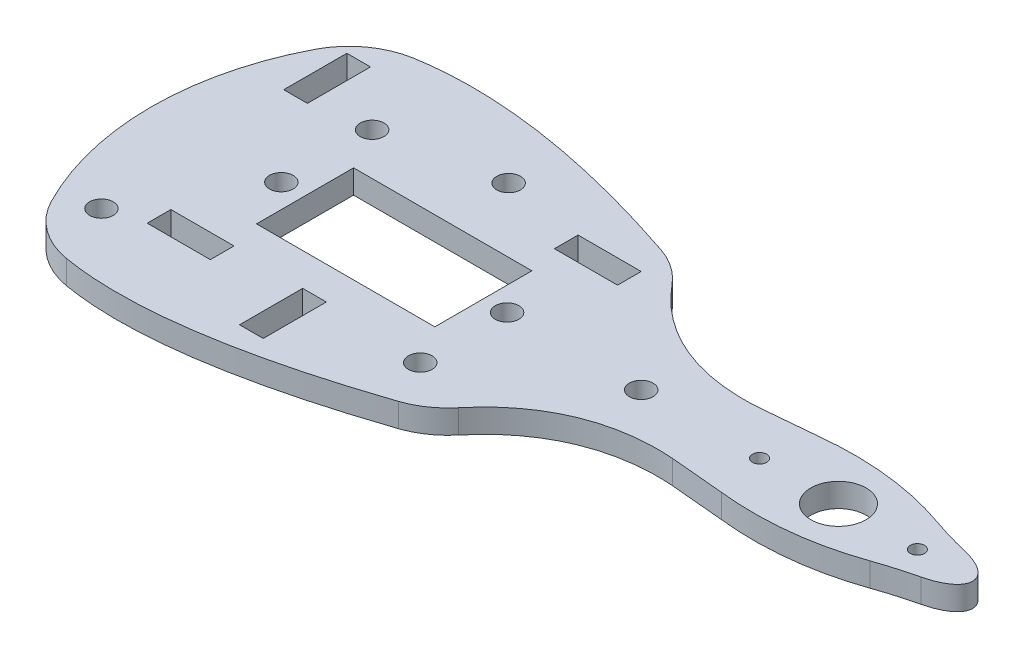
SolidWorks part; units mm, degrees
ref_plane "Plano frontal" through (0, 0, 0) normal (0, 0, 1) x (1, 0, 0)
ref_plane "Plano superior" through (0, 0, 0) normal (0, 1, 0) x (1, 0, 0)
ref_plane "Plano direito" through (0, 0, 0) normal (1, 0, 0) x (0, 0, -1)
sketch "Esboço1" plane through (0, 0, 0) normal (0, 1, 0) x (1, 0, 0)
  line L0 (-56.742, 5.7499) -> (-56.742, -6.5501)
  line L1 (-56.742, 5.7499) -> (-34.142, 5.7499)
  line L2 (-34.142, 5.7499) -> (-34.142, -6.5501)
  line L3 (-34.142, -6.5501) -> (-56.742, -6.5501)
  line L4 (-46.742, -10.7001) -> (-43.742, -10.7001)
  line L5 (-43.742, -10.7001) -> (-43.742, -18.7001)
  line L6 (-43.742, -18.7001) -> (-46.742, -18.7001)
  line L7 (-46.742, -18.7001) -> (-46.742, -10.7001)
  line L8 (-66.742, 9.8999) -> (-69.742, 9.8999)
  line L9 (-69.742, 9.8999) -> (-69.742, 17.8999)
  line L10 (-69.742, 17.8999) -> (-66.742, 17.8999)
  line L11 (-66.742, 17.8999) -> (-66.742, 9.8999)
  line L12 (-35.142, 9.5999) -> (-35.142, 12.5999)
  line L13 (-35.142, 12.5999) -> (-27.142, 12.5999)
  line L14 (-27.142, 12.5999) -> (-27.142, 9.5999)
  line L15 (-27.142, 9.5999) -> (-35.142, 9.5999)
  line L16 (-55.742, -10.4001) -> (-55.742, -13.4001)
  line L17 (-55.742, -13.4001) -> (-63.742, -13.4001)
  line L18 (-63.742, -13.4001) -> (-63.742, -10.4001)
  line L19 (-63.742, -10.4001) -> (-55.742, -10.4001)
  line L20 (-34.142, -0.4001) -> (-39.142, -0.4001)
  line L21 (118.7091, -104.6007) -> (118.7091, -116.9007)
  line L43 (-4.6744, 5.1268) -> (2.1565, 5.7499)
  line L44 (2.1565, -6.5501) -> (-4.6744, -5.927)
  line L45 (118.7091, -104.6007) -> (141.3091, -104.6007)
  line L46 (141.3091, -104.6007) -> (141.3091, -116.9007)
  line L47 (141.3091, -116.9007) -> (118.7091, -116.9007)
  line L48 (128.7091, -121.0507) -> (131.7091, -121.0507)
  line L49 (131.7091, -121.0507) -> (131.7091, -129.0507)
  line L50 (131.7091, -129.0507) -> (128.7091, -129.0507)
  line L51 (128.7091, -129.0507) -> (128.7091, -121.0507)
  line L52 (108.7091, -100.4507) -> (105.7091, -100.4507)
  line L53 (105.7091, -100.4507) -> (105.7091, -92.4507)
  line L54 (105.7091, -92.4507) -> (108.7091, -92.4507)
  line L55 (108.7091, -92.4507) -> (108.7091, -100.4507)
  line L56 (140.3091, -100.7507) -> (140.3091, -97.7507)
  line L57 (140.3091, -97.7507) -> (148.3091, -97.7507)
  line L58 (148.3091, -97.7507) -> (148.3091, -100.7507)
  line L59 (148.3091, -100.7507) -> (140.3091, -100.7507)
  line L60 (119.7091, -120.7507) -> (119.7091, -123.7507)
  line L61 (119.7091, -123.7507) -> (111.7091, -123.7507)
  line L62 (111.7091, -123.7507) -> (111.7091, -120.7507)
  line L63 (111.7091, -120.7507) -> (119.7091, -120.7507)
  line L64 (99.1934, -77.682) -> (151.6919, -77.682)
  line L65 (79.5474, -88.7637) -> (79.5474, -132.7378)
  circle A0 centre (-59.742, -0.4001) radius 1.5
  circle A1 centre (-31.142, -0.4001) radius 1.5
  circle A2 centre (-45.242, 13.8999) radius 1.5
  circle A3 centre (-68.242, -14.7001) radius 1.5
  circle A4 centre (-59.742, 11.0999) radius 1.5
  circle A5 centre (-31.142, -11.4018) radius 1.5
  circle A6 centre (10.858, -0.4001) radius 3.5
  arc A9 (-72.1928, 16.3196) -> (-72.1928, -17.1198) centre (-39.8393, -0.4001) ccw
  arc A10 (-72.1928, 16.3196) -> (-64.9861, 21.587) centre (-63.309, 11.7286) cw
  arc A14 (24.1011, 2.407) -> (19.1277, 3.8594) centre (35.6119, 51.064) cw
  arc A15 (19.1277, -4.6595) -> (24.1011, -3.2071) centre (35.6119, -51.8641) cw
  circle A16 centre (20.858, -0.4001) radius 0.9
  circle A17 centre (0.858, -0.4001) radius 0.9
  circle A25 centre (-14.142, -0.4001) radius 1.5
  circle A26 centre (115.7091, -110.7507) radius 1.5
  circle A27 centre (144.3091, -110.7507) radius 1.5
  circle A28 centre (130.2091, -96.4507) radius 1.5
  arc A29 (-72.1928, -17.1198) -> (-64.9861, -22.3871) centre (-63.309, -12.5288) ccw
  arc A30 (-28.2773, -17.0396) -> (-23.759, -13.9261) centre (-31.4747, -7.5646) ccw
  arc A31 (-28.2773, 16.2395) -> (-23.759, 13.1259) centre (-31.4747, 6.7644) cw
  circle A32 centre (107.2091, -125.0507) radius 1.5
  circle A33 centre (115.7091, -99.2507) radius 1.5
  circle A34 centre (144.3091, -121.7524) radius 1.5
  arc A35 (103.2583, -94.031) -> (103.2583, -127.4704) centre (135.6118, -110.7507) ccw
  arc A36 (103.2583, -94.031) -> (110.465, -88.7637) centre (112.1421, -98.622) cw
  arc A37 (103.2583, -127.4704) -> (110.465, -132.7378) centre (112.1421, -122.8794) ccw
  arc A38 (147.1738, -127.3903) -> (151.6921, -124.2767) centre (143.9764, -117.9152) ccw
  arc A39 (147.1738, -94.1112) -> (151.6919, -97.2247) centre (143.9763, -103.5862) cw
  ellipse E0 centre (20.858, -0.4001) end of major axis (27.858, -0.4001) minor radius 3.1675 (24.1011, -3.2071) -> (24.1011, 2.407) ccw
  spline S0 degree 3 poles (19.1277, 3.8594) (13.6929, 5.7573) (8.0358, 6.3875) (2.1565, 5.7499) knots 0.353889 0.353889 0.353889 0.353889 1 1 1 1
  spline S1 degree 3 poles (147.1738, -94.1112) (140.8719, -91.9845) (127.8533, -88.4031) (115.8008, -87.8559) (110.465, -88.7637) knots 0.24159 0.24159 0.24159 0.24159 0.401358 0.561127 0.561127 0.561127 0.561127
  spline S2 degree 3 poles (-28.2773, 16.2395) (-34.5792, 18.3661) (-47.5978, 21.9476) (-59.6503, 22.4947) (-64.9861, 21.587) knots 0.24159 0.24159 0.24159 0.24159 0.401358 0.561127 0.561127 0.561127 0.561127
  spline S3 degree 3 poles (-28.2773, -17.0396) (-34.5792, -19.1662) (-47.5978, -22.7477) (-59.6503, -23.2949) (-64.9861, -22.3871) knots 0.24159 0.24159 0.24159 0.24159 0.401358 0.561127 0.561127 0.561127 0.561127
  spline S4 degree 3 poles (147.1738, -127.3903) (140.8719, -129.5169) (127.8533, -133.0983) (115.8008, -133.6455) (110.465, -132.7378) knots 0.24159 0.24159 0.24159 0.24159 0.401358 0.561127 0.561127 0.561127 0.561127
  spline S5 degree 3 poles (19.1277, -4.6595) (13.6929, -6.5574) (8.0358, -7.1876) (2.1565, -6.5501) knots 0.353889 0.353889 0.353889 0.353889 1 1 1 1
  spline S9 degree 3 poles (-23.759, 13.1259) (-18.9931, 7.3456) (-12.4241, 4.5674) (-4.6744, 5.1268) knots 0.101822 0.101822 0.101822 0.101822 1 1 1 1
  spline S10 degree 3 poles (-23.759, -13.9261) (-18.9931, -8.1457) (-12.4241, -5.3676) (-4.6744, -5.927) knots 0.101822 0.101822 0.101822 0.101822 1 1 1 1
  dimension "D1" = 10
  dimension "D2" = 10
  dimension "D3" = 52.4985
  dimension "D4" = 43.9741
  dimension "D5" = 10
  dimension "D10" = 3
  dimension "D8" = 22.6
  dimension "D9" = 12.3
  dimension "D11" = 8
  dimension "D12" = 3
extrude "Ressalto-extrusão1" add sketch "Esboço1" along normal blind 3
